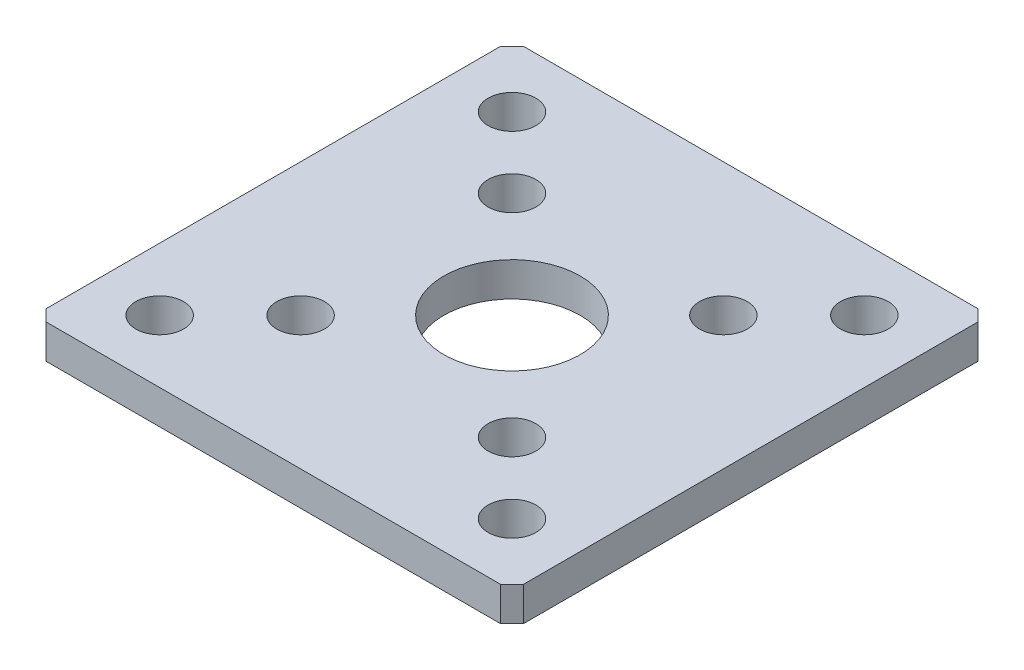
SolidWorks part; units mm, degrees
ref_plane "Front" through (0, 0, 0) normal (0, 0, 1) x (1, 0, 0)
ref_plane "Top" through (0, 0, 0) normal (0, 1, 0) x (1, 0, 0)
ref_plane "Right" through (0, 0, 0) normal (1, 0, 0) x (0, 0, -1)
sketch "草圖1" plane through (0, 0, 0) normal (0, 1, 0) x (1, 0, 0)
  line L1 (-21, -21) -> (21, -21)
  line L2 (-21, -21) -> (-21, 21)
  line L3 (-21, 21) -> (21, 21)
  line L4 (21, -21) -> (21, 21)
  line L5 (-21, -21) -> (21, 21) construction
  line L6 (-21, 21) -> (21, -21) construction
  point P0 (0, 0)
  dimension "D1" = 42
extrude "填料-伸長1" add sketch "草圖1" along normal blind 3
sketch "草圖2" plane through (0, 0, 0) normal (0, -1, 0) x (1, 0, 0)
  circle A0 centre (0, 0) radius 6
  dimension "D1" = 12
extrude "除料-伸長1" cut sketch "草圖2" against normal through all
sketch "草圖4" plane through (0, 3, 0) normal (0, 1, 0) x (1, 0, 0)
  line L1 (0, 0) -> (0, 9.3) construction
  line L2 (0, 9.3) -> (-9.3, 9.3) construction
  circle A0 centre (-9.3, 9.3) radius 2.1
  dimension "D2" = 4.2
  dimension "D1" = 9.3
extrude "除料-伸長2" cut sketch "草圖4" against normal through all
sketch "草圖5" plane through (0, 3, 0) normal (0, 1, 0) x (1, 0, 0)
  line L0 (0, 0) -> (0, 15.5) construction
  line L1 (0, 15.5) -> (-15.5, 15.5) construction
  circle A0 centre (-15.5, 15.5) radius 2.1
  dimension "D2" = 4.2
  dimension "D1" = 15.5
extrude "除料-伸長3" cut sketch "草圖5" against normal through all
pattern_circular "環狀複製排列1" count 4 over 360 about axis through (0, 0, 0) along (0, 1, 0) of "除料-伸長3", "除料-伸長2"
chamfer "導角1" distance 1 angle 45 4 edges at (21, 1.5, -21) (21, 1.5, 21) (-21, 1.5, 21) (-21, 1.5, -21)
